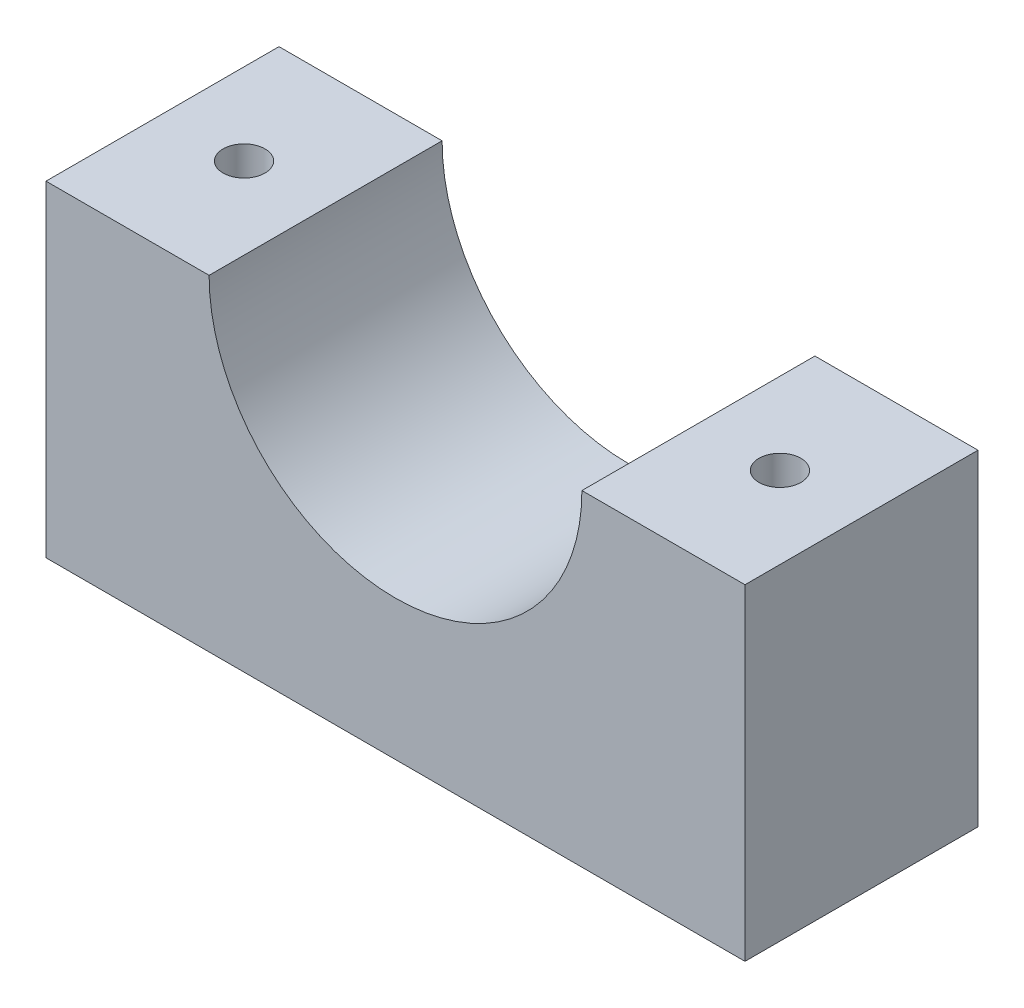
SolidWorks part; units mm, degrees
ref_plane "Front Plane" through (0, 0, 0) normal (0, 0, 1) x (1, 0, 0)
ref_plane "Top Plane" through (0, 0, 0) normal (0, 1, 0) x (1, 0, 0)
ref_plane "Right Plane" through (0, 0, 0) normal (1, 0, 0) x (0, 0, -1)
sketch "Sketch1" plane through (0, 0, 0) normal (0, 0, 1) x (1, 0, 0)
  line L1 (0, 0) -> (38.1, 0)
  line L2 (0, 0) -> (0, -17.78)
  line L3 (0, -17.78) -> (38.1, -17.78)
  line L4 (38.1, 0) -> (38.1, -17.78)
  dimension "D1" = 38.1
  dimension "D2" = 17.78
extrude "Boss-Extrude1" add sketch "Sketch1" along normal blind 12.7
sketch "Sketch4" plane through (0, 0, 12.7) normal (0, 0, 1) x (1, 0, 0)
  line L0 (19.05, 0) -> (29.21, 0)
  line L1 (38.1, 0) -> (0, 0) construction
  line L2 (19.05, 0) -> (8.89, 0)
  arc A0 (8.89, 0) -> (29.21, 0) centre (19.05, 0) ccw
extrude "Cut-Extrude1" cut sketch "Sketch4" against normal through all
sketch "Sketch5" plane through (0, 0, 0) normal (0, 1, 0) x (1, 0, 0)
  line L0 (0, 0) -> (0, -6.35)
  line L1 (0, -12.7) -> (0, 0) construction
  line L2 (0, -6.35) -> (8.89, -6.35)
  line L3 (8.89, 0) -> (8.89, -12.7) construction
  line L4 (38.1, 0) -> (38.1, -6.35)
  line L5 (38.1, -12.7) -> (38.1, 0) construction
  line L6 (38.1, -6.35) -> (29.21, -6.35)
  line L7 (29.21, 0) -> (29.21, -12.7) construction
  circle A0 centre (4.445, -6.35) radius 1.143
  circle A1 centre (33.655, -6.35) radius 1.143
  dimension "D1" = 2.286
  dimension "D2" = 2.286
extrude "Cut-Extrude2" cut sketch "Sketch5" against normal through all contours L2 A0 | L2 A0 | L6 A1 | L6 A1
